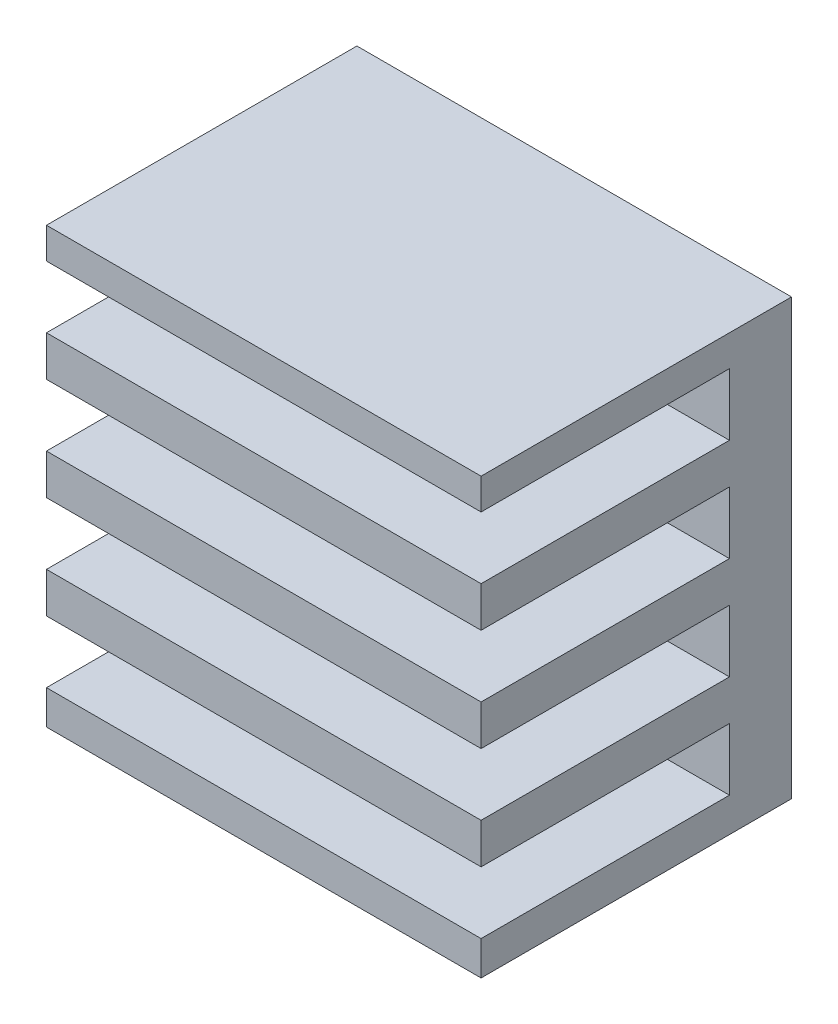
SolidWorks part; units mm, degrees
ref_plane "Front Plane" through (0, 0, 0) normal (0, 0, 1) x (1, 0, 0)
ref_plane "Top Plane" through (0, 0, 0) normal (0, 1, 0) x (1, 0, 0)
ref_plane "Right Plane" through (0, 0, 0) normal (1, 0, 0) x (0, 0, -1)
sketch "Sketch1" plane through (0, 0, 0) normal (0, 0, 1) x (1, 0, 0)
  line L1 (16.5, 34.5) -> (30.5, 34.5)
  line L2 (16.5, 34.5) -> (16.5, 20.5)
  line L3 (16.5, 20.5) -> (30.5, 20.5)
  line L4 (30.5, 34.5) -> (30.5, 20.5)
extrude "Boss-Extrude1" add sketch "Sketch1" along normal blind 10
sketch "Sketch2" plane through (16.5, 0, 0) normal (-1, 0, 0) x (0, 0, 1)
  line L0 (10, 34.5) -> (10, 20.5) construction
  line L1 (10, 33.5) -> (2, 33.5)
  line L2 (10, 33.5) -> (10, 31.5)
  line L3 (10, 31.5) -> (2, 31.5)
  line L4 (2, 33.5) -> (2, 31.5)
  line L5 (10, 34.5) -> (0, 34.5) construction
  line L6 (0, 34.5) -> (0, 20.5) construction
  line L7 (10, 30.2) -> (2, 30.2)
  line L8 (10, 30.2) -> (10, 28.2)
  line L9 (10, 28.2) -> (2, 28.2)
  line L10 (2, 30.2) -> (2, 28.2)
  line L11 (10, 26.9) -> (2, 26.9)
  line L12 (10, 26.9) -> (10, 24.9)
  line L13 (10, 24.9) -> (2, 24.9)
  line L14 (2, 26.9) -> (2, 24.9)
  line L15 (10, 23.6) -> (2, 23.6)
  line L16 (10, 23.6) -> (10, 21.6)
  line L17 (10, 21.6) -> (2, 21.6)
  line L18 (2, 23.6) -> (2, 21.6)
  dimension "D1" = 2
  dimension "D2" = 1
  dimension "D3" = 2
  dimension "D4" = 4
extrude "Cut-Extrude1" cut sketch "Sketch2" against normal through all
